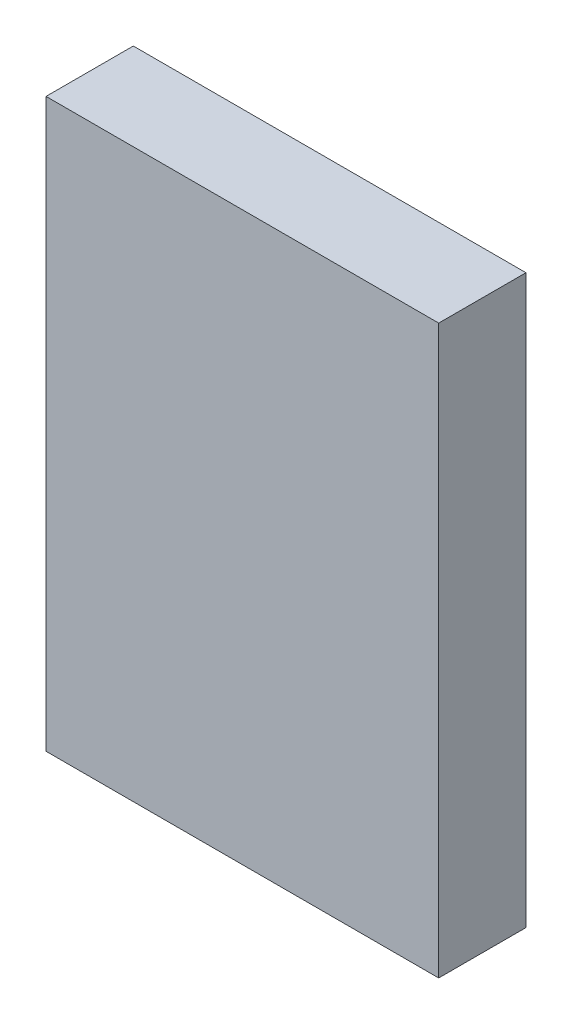
SolidWorks part; units mm, degrees
ref_plane "Plan de face" through (0, 0, 0) normal (0, 0, 1) x (1, 0, 0)
ref_plane "Plan de dessus" through (0, 0, 0) normal (0, 1, 0) x (1, 0, 0)
ref_plane "Plan de droite" through (0, 0, 0) normal (1, 0, 0) x (0, 0, -1)
sketch "Esquisse1" plane through (0, 0, 0) normal (0, 0, 1) x (1, 0, 0)
  line L1 (-2.25, 3.25) -> (2.25, 3.25)
  line L2 (-2.25, 3.25) -> (-2.25, -3.25)
  line L3 (-2.25, -3.25) -> (2.25, -3.25)
  line L4 (2.25, 3.25) -> (2.25, -3.25)
  line L5 (-2.25, 3.25) -> (2.25, -3.25) construction
  line L6 (-2.25, -3.25) -> (2.25, 3.25) construction
  point P0 (0, 0)
  dimension "D1" = 4.5
  dimension "D2" = 6.5
extrude "Boss.-Extru.1" add sketch "Esquisse1" along normal blind 1
